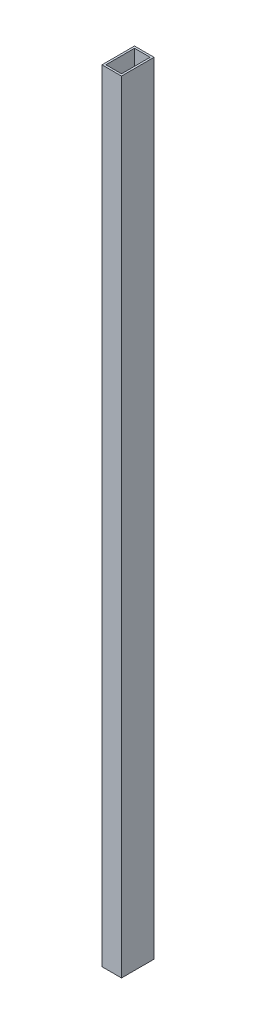
SolidWorks part; units mm, degrees
ref_plane "Front Plane" through (0, 0, 0) normal (0, 0, 1) x (1, 0, 0)
ref_plane "Top Plane" through (0, 0, 0) normal (0, 1, 0) x (1, 0, 0)
ref_plane "Right Plane" through (0, 0, 0) normal (1, 0, 0) x (0, 0, -1)
sketch "Sketch1" plane through (0, 0, 0) normal (0, 1, 0) x (1, 0, 0)
  line L0 (7.62, 7.62) -> (68.58, 7.62)
  line L1 (0, 0) -> (76.2, 0)
  line L2 (0, 0) -> (0, 127)
  line L3 (0, 127) -> (76.2, 127)
  line L4 (76.2, 0) -> (76.2, 127)
  line L5 (68.58, 7.62) -> (68.58, 119.38)
  line L6 (7.62, 119.38) -> (68.58, 119.38)
  line L7 (7.62, 7.62) -> (7.62, 119.38)
  dimension "D1" = 127
  dimension "D2" = 76.2
  dimension "D3" = 7.62
extrude "Boss-Extrude1" add sketch "Sketch1" along normal blind 3048
